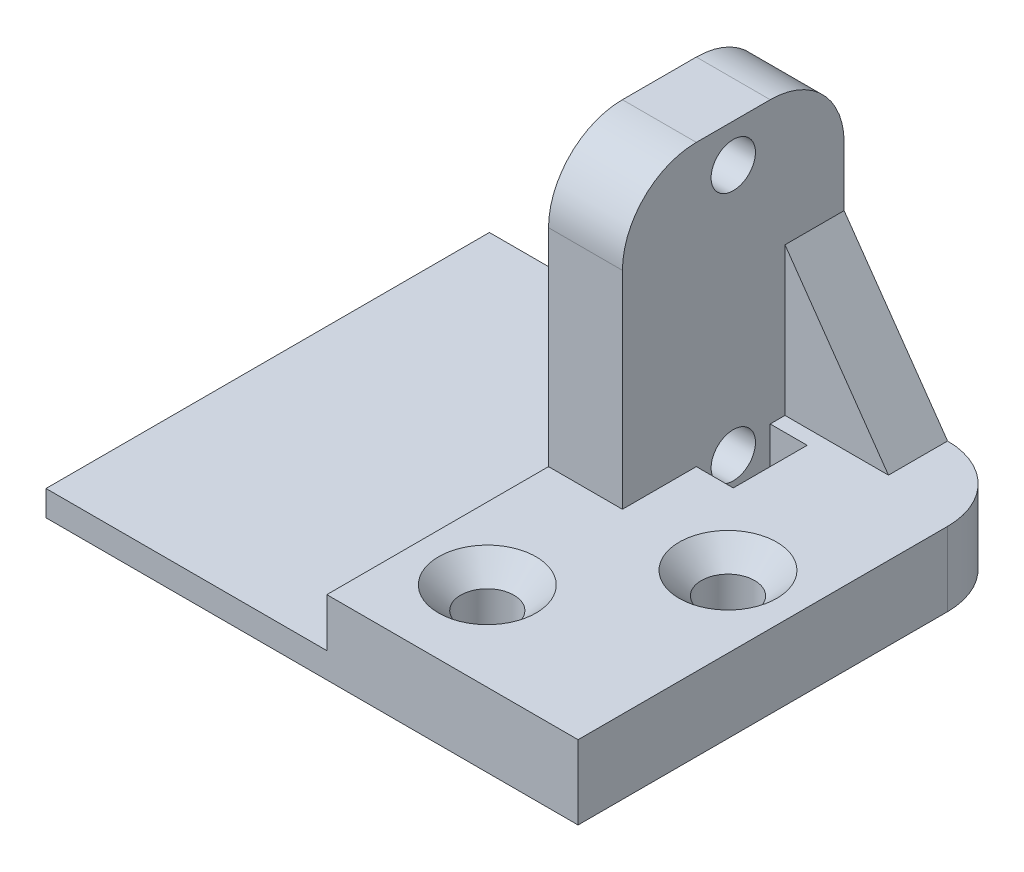
SolidWorks part; units mm, degrees
ref_plane "前视基准面" through (0, 0, 0) normal (0, 0, 1) x (1, 0, 0)
ref_plane "上视基准面" through (0, 0, 0) normal (0, 1, 0) x (1, 0, 0)
ref_plane "右视基准面" through (0, 0, 0) normal (1, 0, 0) x (0, 0, -1)
sketch "草图1" plane through (0, 0, 0) normal (1, 0, 0) x (0, 0, -1)
  line L0 (0, 0) -> (0, 24) construction
  line L1 (-7.5, 24) -> (7.5, 24)
  line L2 (-7.5, 24) -> (-7.5, 0)
  line L3 (-7.5, 0) -> (7.5, 0)
  line L4 (7.5, 24) -> (7.5, 0)
  line L6 (-7.5, 1.92) -> (7.5, 1.92) construction
  circle A0 centre (0, 4.42) radius 1.5
  circle A1 centre (0, 21.42) radius 1.5
  dimension "D1" = 3
  dimension "D2" = 17
  dimension "D3" = 4.42
  dimension "D4" = 15
  dimension "D6" = 24
  dimension "D7" = 1.92
extrude "凸台-拉伸1" add sketch "草图1" along normal blind 5
sketch "草图2" plane through (0, 0, 0) normal (-1, 0, 0) x (0, 0, 1)
  line L0 (-7.5, 0) -> (-7.5, 24) construction
  line L1 (22.5, 0) -> (-7.5, 0)
  line L2 (22.5, 0) -> (22.5, 1.72)
  line L3 (22.5, 1.72) -> (-7.5, 1.72)
  line L4 (-7.5, 0) -> (-7.5, 1.72)
  line L6 (7.5, 0) -> (-7.5, 0) construction
  dimension "D1" = 30
  dimension "D2" = 1.72
extrude "凸台-拉伸2" add sketch "草图2" along normal blind 19
sketch "草图4" plane through (0, 0, 0) normal (0, 1, 0) x (1, 0, 0)
  line L1 (5, 7.5) -> (17, 7.5)
  line L2 (5, 7.5) -> (5, -7.5)
  line L3 (0, -22.5) -> (17, -22.5)
  line L4 (17, 7.5) -> (17, -22.5)
  line L5 (-19, -22.5) -> (0, -22.5) construction
  line L6 (0, -7.5) -> (0, -22.5) construction
  line L7 (5, -7.5) -> (0, -7.5) construction
  line L8 (0, -7.5) -> (0, -22.5)
  line L9 (5, -7.5) -> (0, -7.5)
  dimension "D1" = 12
extrude "凸台-拉伸5" add sketch "草图4" along normal blind 5
sketch "草图7" plane through (0, 5, 0) normal (0, 1, 0) x (1, 0, 0)
  line L0 (0, 0) -> (9.2745, 0) construction
  line L2 (5, -2.5) -> (7.5, -2.5)
  line L3 (5, -2.5) -> (5, 2.5)
  line L4 (5, 2.5) -> (7.5, 2.5)
  line L5 (7.5, -2.5) -> (7.5, 2.5)
  line L6 (5, 7.5) -> (5, -7.5) construction
  dimension "D1" = 5
  dimension "D2" = 2.5
extrude "切除-拉伸1" cut sketch "草图7" against normal blind 3
fillet "圆角1" radius 5 3 edges at (2.5, 24, -7.5) (2.5, 24, 7.5) (17, 2.5, -7.5)
hole_wizard "打孔尺寸(%根据十字)槽半沉头木螺钉的类型1" positions "草图8" profile "草图9" countersink size "M3" standard "GB" end condition through all
sketch "草图8" plane through (0, 5, 0) normal (0, 1, 0) x (1, 0, 0)
  line L0 (0, -22.5) -> (17, -1.5) construction
  line L1 (17, -22.5) -> (17, 2.5) construction
  line L5 (0, -22.5) -> (17, -22.5) construction
  point P0 (4.8571, -16.5)
  point P2 (12.1429, -7.5)
  point P15 (0, 0)
  point P16 (0, 0)
  point P17 (0, 0)
  point P20 (0, 0)
  dimension "D1" = 21
  dimension "D2" = 6
  dimension "D3" = 6
sketch "草图9" plane through (4.8571, 5, 16.5) normal (1, 0, 0) x (0, 0, 1)
  line L0 (0, 0) -> (0, 5)
  line L1 (0, 5) -> (1.8, 5)
  line L2 (1.8, 5) -> (1.8, 1.5)
  line L3 (1.8, 1.5) -> (3.3, 0)
  line L5 (3.3, 0) -> (0, 0)
  line L6 (-1.8, 1.5) -> (-3.3, 0) construction
  line L11 (0, -6.35) -> (0, 107.95) construction
  dimension "通孔孔直径" = 3.6
  dimension "通孔孔深度" = 5
  dimension "近端锥形沉头孔直径" = 6.6
  dimension "近端锥形沉头孔角度" = 90
sketch "草图10" plane through (0, 0, -7.5) normal (0, 0, -1) x (-1, 0, 0)
  line L0 (-12, 5) -> (-5, 15)
  line L1 (-5, 5) -> (-5, 19) construction
  line L2 (-12, 5) -> (-5, 5) construction
  dimension "D1" = 10
rib "筋1" sketch "草图10" sketch "草图10" thickness 4 extrusion direction parallel to sketch draft on no parameters "D1"=4
